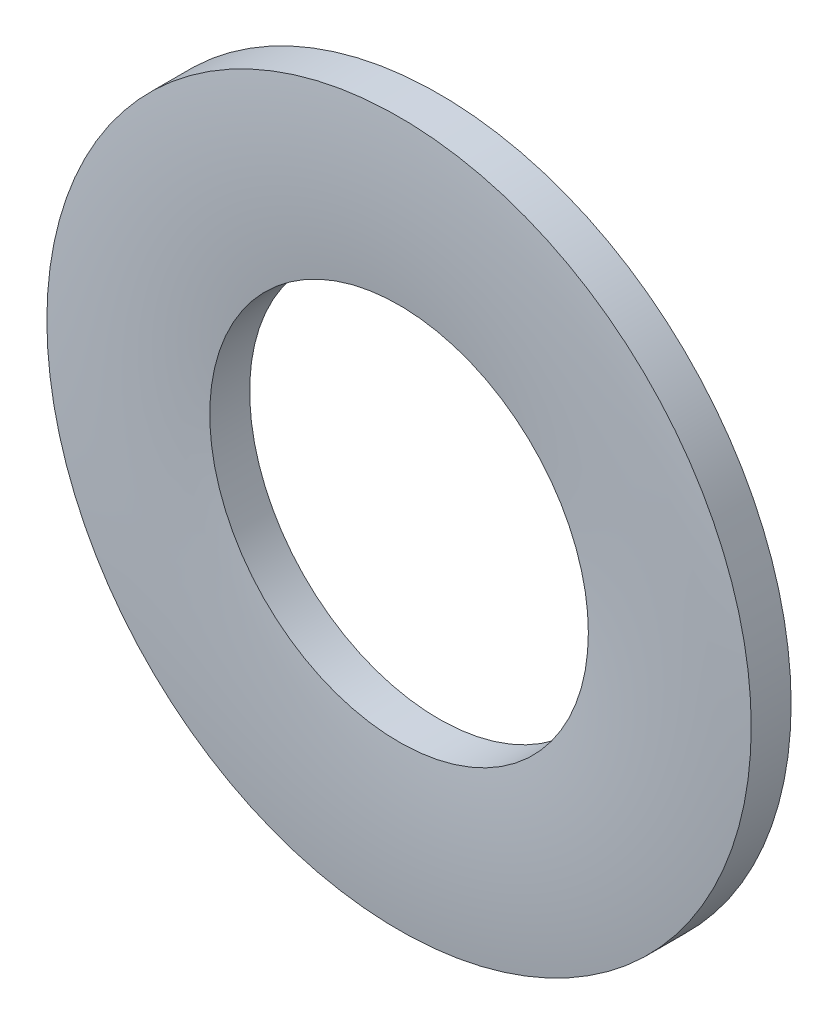
SolidWorks part; units mm, degrees
material "Plain Carbon Steel"
ref_plane "Front Plane" through (0, 0, 0) normal (0, 0, 1) x (1, 0, 0)
ref_plane "Top Plane" through (0, 0, 0) normal (0, 1, 0) x (1, 0, 0)
ref_plane "Right Plane" through (0, 0, 0) normal (1, 0, 0) x (0, 0, -1)
sketch "Sketch1" plane through (0, 0, 0) normal (0, 0, 1) x (1, 0, 0)
  circle A0 centre (0, 0) radius 2.15
  circle A1 centre (0, 0) radius 4
  dimension "ID" = 4.3
  dimension "OD" = 8
sketch "Sketch2" plane through (0, 0, 0) normal (1, 0, 0) x (0, 0, -1)
  line L0 (-0.25, 4) -> (0.25, 4) construction
  line L1 (-0.25, 0) -> (0.25, 0) construction
  point P2 (0, 4)
  dimension "Thickness Range" = 0.5
sketch "Sketch3" plane through (0, 0, 0) normal (1, 0, 0) x (0, 0, -1)
  line L0 (0.25, 4) -> (-0.2031, 4)
  line L1 (0.25, 2.15) -> (-0.2031, 2.15)
  line L2 (0.25, 2.15) -> (0.25, 4)
  line L3 (-0.25, 4) -> (-0.25, 2.15) construction
  arc A0 (-0.2031, 2.15) -> (-0.2031, 4) centre (8.905, 3.075) cw
  point P9 (0, 2.15)
  dimension "D1" = 0.0469
revolve "Revolve1" add sketch "Sketch3" angle 360 about L1
ref_plane "Plane1" through (0, 0, -0.25) normal (0, 0, -1) x (-1, 0, 0)
ref_plane "Plane2" through (0, 0, 0.25) normal (0, 0, -1) x (-1, 0, 0)
equation "\"D1@Sketch3\"=\"Thickness Range@Sketch2\"*.0937"
